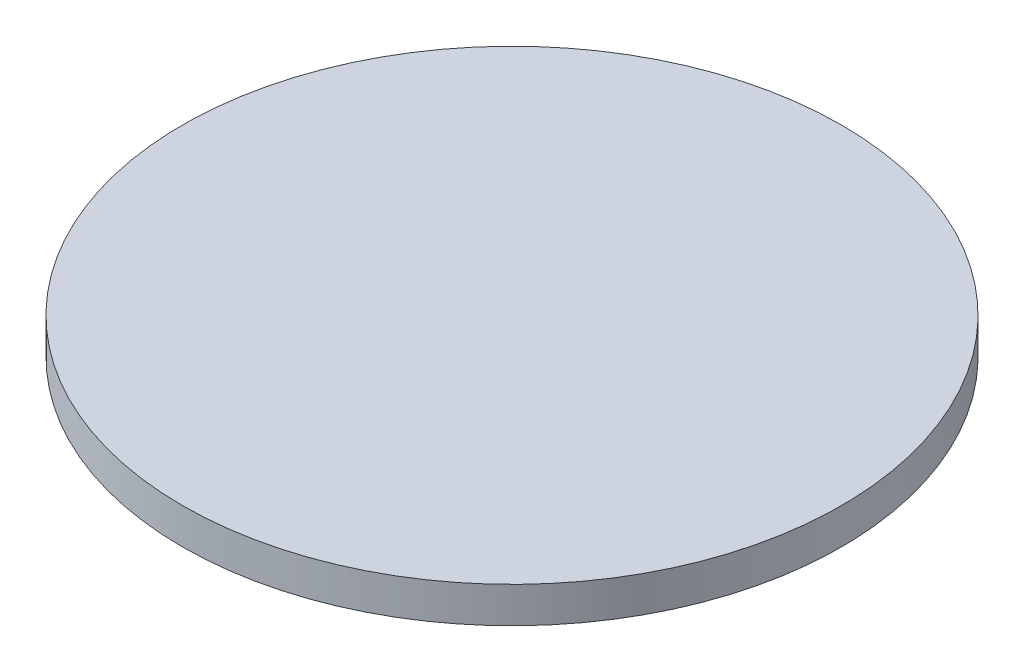
SolidWorks part; units mm, degrees
ref_plane "前视基准面" through (0, 0, 0) normal (0, 0, 1) x (1, 0, 0)
ref_plane "上视基准面" through (0, 0, 0) normal (0, 1, 0) x (1, 0, 0)
ref_plane "右视基准面" through (0, 0, 0) normal (1, 0, 0) x (0, 0, -1)
sketch "草图1" plane through (0, 0, 0) normal (0, 1, 0) x (1, 0, 0)
  circle A0 centre (0, 0) radius 12.5
  dimension "D1" = 25
extrude "凸台-拉伸1" add sketch "草图1" along normal blind 1.36
